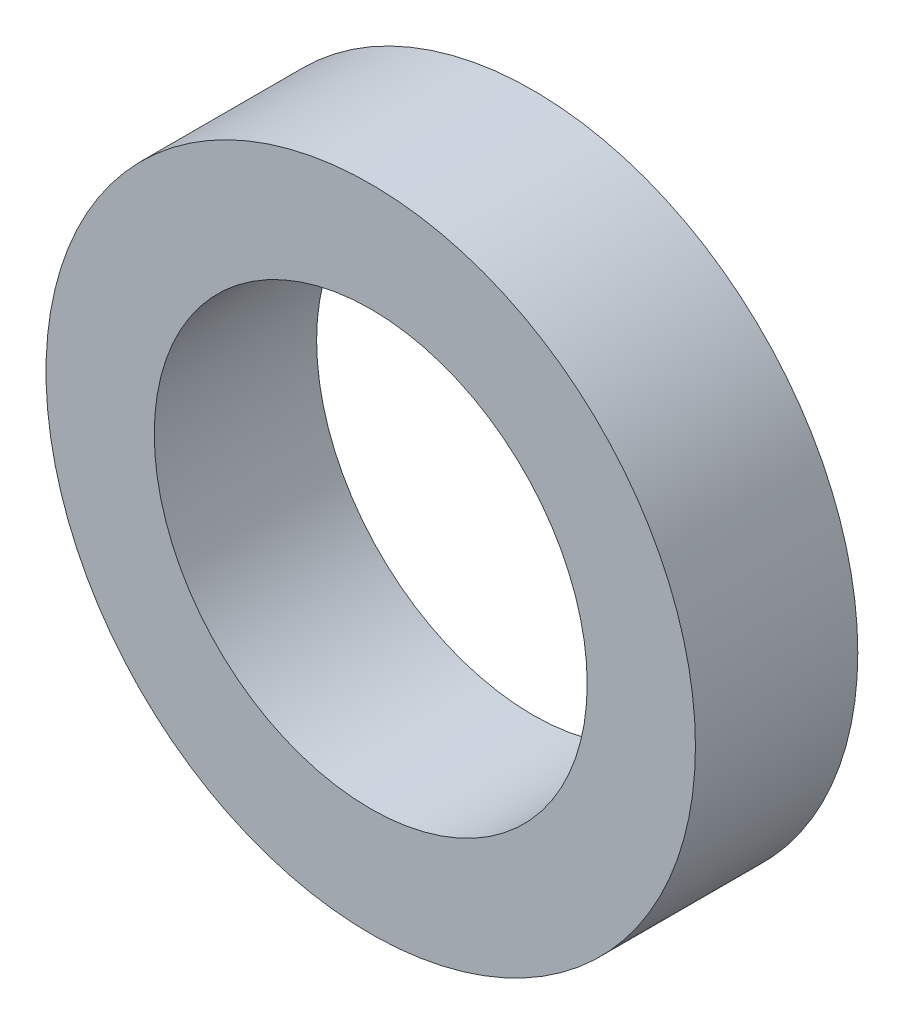
SolidWorks part; units mm, degrees
ref_plane "Front Plane" through (0, 0, 0) normal (0, 0, 1) x (1, 0, 0)
ref_plane "Top Plane" through (0, 0, 0) normal (0, 1, 0) x (1, 0, 0)
ref_plane "Right Plane" through (0, 0, 0) normal (1, 0, 0) x (0, 0, -1)
sketch "Sketch1" plane through (0, 0, 0) normal (0, 0, 1) x (1, 0, 0)
  circle A0 centre (0, 0) radius 4
  circle A1 centre (0, 0) radius 6
  dimension "D1" = 8
  dimension "D2" = 12
extrude "Boss-Extrude1" add sketch "Sketch1" along normal blind 3
